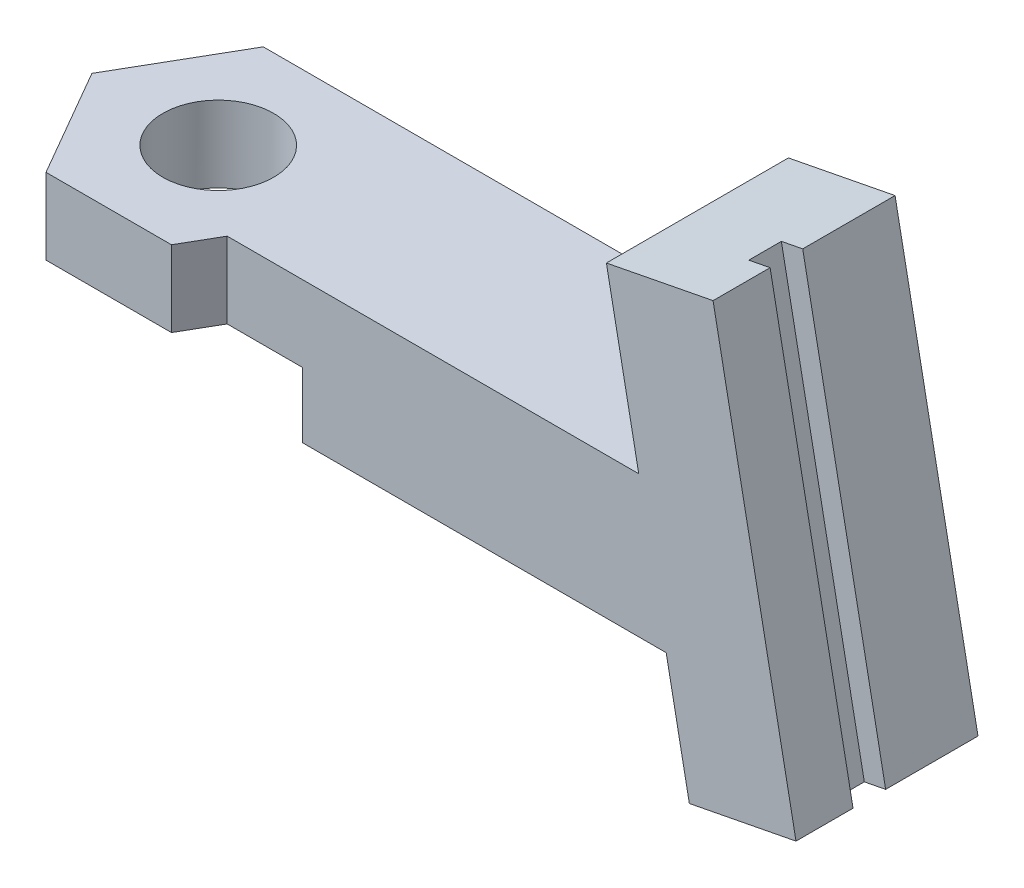
SolidWorks part; units mm, degrees
ref_plane "Front Plane" through (0, 0, 0) normal (0, 0, 1) x (1, 0, 0)
ref_plane "Top Plane" through (0, 0, 0) normal (0, 1, 0) x (1, 0, 0)
ref_plane "Right Plane" through (0, 0, 0) normal (1, 0, 0) x (0, 0, -1)
sketch "Sketch1" plane through (0, 0, 0) normal (0, 1, 0) x (1, 0, 0)
  line L1 (0, 0) -> (25, 0)
  line L2 (0, 0) -> (0, -6.75)
  line L3 (0, -6.75) -> (25, -6.75)
  line L4 (25, 0) -> (25, -6.75)
  dimension "D1" = 6.75
  dimension "D2" = 25
extrude "Boss-Extrude1" add sketch "Sketch1" along normal blind 6.5
ref_plane "Plane1" through (0, 0, 3.375) normal (0, 0, 1) x (1, 0, 0)
sketch "Sketch3" plane through (0, 0, 3.375) normal (0, 0, 1) x (1, 0, 0)
  line L0 (21.2757, 14.1555) -> (26.1838, 15.1096)
  line L1 (26.1838, 15.1096) -> (30, -4.523)
  line L2 (30, -4.523) -> (25.0919, -5.477)
  line L3 (25.0919, -5.477) -> (21.2757, 14.1555)
  line L4 (0, 6.5) -> (25, 6.5) construction
  line L5 (0, 6.5) -> (0, 0) construction
  point P6 (27.5459, -5)
  dimension "D1" = 30
  dimension "D2" = 5
  dimension "D3" = 20
  dimension "D4" = 79
  dimension "D6" = 5
extrude "Boss-Extrude3" add sketch "Sketch3" against normal up to surface and the other way up to surface
sketch "Sketch4" plane through (-1.8768, 9.6551, 0) normal (-0.1908, 0.9816, 0) x (0.9816, 0.1908, 0)
  line L0 (28.5858, -6.75) -> (28.5858, 0) construction
  line L1 (27.5858, -2.625) -> (28.5858, -2.625)
  line L2 (27.5858, -2.625) -> (27.5858, -4.125)
  line L3 (27.5858, -4.125) -> (28.5858, -4.125)
  line L4 (28.5858, -2.625) -> (28.5858, -4.125)
  point P6 (28.5858, -3.375)
  dimension "D1" = 1.5
  dimension "D2" = 1
extrude "Cut-Extrude1" cut sketch "Sketch4" against normal blind 23 contours L2 L3 L4 L1
sketch "Sketch5" plane through (0, 6.5, 0) normal (0, 1, 0) x (1, 0, 0)
  line L0 (0, 0) -> (0, -6.75) construction
  line L1 (-5.7735, -3.375) -> (-2.8868, -8.375)
  line L2 (-2.8868, -8.375) -> (2.8868, -8.375)
  line L3 (2.8868, -8.375) -> (5.7735, -3.375)
  line L4 (5.7735, -3.375) -> (2.8868, 1.625)
  line L5 (2.8868, 1.625) -> (-2.8868, 1.625)
  line L6 (-2.8868, 1.625) -> (-5.7735, -3.375)
  circle A0 centre (0, -3.375) radius 5 construction
  dimension "D1" = 5
extrude "Boss-Extrude4" add sketch "Sketch5" against normal up to surface (6.5 mm away)
sketch "Sketch6" plane through (0, 6.5, 0) normal (0, 1, 0) x (1, 0, 0)
  circle A0 centre (0, -3.3356) radius 2.55
  dimension "D1" = 5.1
extrude "Cut-Extrude2" cut sketch "Sketch6" against normal blind 10
sketch "Sketch7" plane through (0, 0, -1.625) normal (0, 0, -1) x (-1, 0, 0)
  line L0 (-2.8868, 0) -> (-24.0272, 0)
  line L1 (-24.0272, 0) -> (-25.0919, -5.477)
  line L2 (-25.0919, -5.477) -> (-30, -4.523)
  line L3 (-30, -4.523) -> (-26.1838, 15.1096)
  line L4 (-26.1838, 15.1096) -> (-21.2757, 14.1555)
  line L5 (-21.2757, 14.1555) -> (-22.7638, 6.5)
  line L6 (-22.7638, 6.5) -> (-2.8868, 6.5)
  line L7 (-2.8868, 6.5) -> (-2.8868, 0)
extrude "Boss-Extrude5" add sketch "Sketch7" against normal up to surface (1.625 mm away)
sketch "Sketch8" plane through (0, 0, 0) normal (0, -1, 0) x (-1, 0, 0)
  line L1 (-4.6188, -11.375) -> (4.6188, -11.375)
  line L2 (4.6188, -11.375) -> (9.2376, -3.375)
  line L3 (9.2376, -3.375) -> (4.6188, 4.625)
  line L4 (4.6188, 4.625) -> (-4.6188, 4.625)
  line L5 (-4.6188, 4.625) -> (-9.2376, -3.375)
  line L6 (-9.2376, -3.375) -> (-4.6188, -11.375)
  circle A0 centre (0, -3.375) radius 8 construction
  dimension "D1" = 16
extrude "Cut-Extrude3" cut sketch "Sketch8" against normal blind 3
